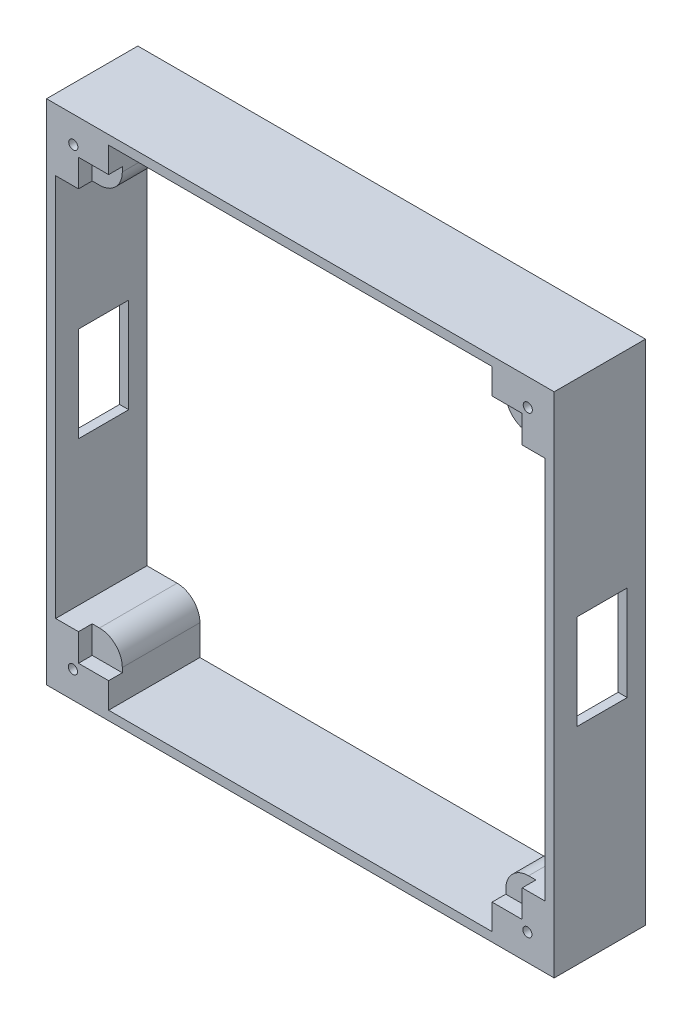
SolidWorks part; units mm, degrees
ref_plane "Přední rovina" through (0, 0, 0) normal (0, 0, 1) x (1, 0, 0)
ref_plane "Horní rovina" through (0, 0, 0) normal (0, 1, 0) x (1, 0, 0)
ref_plane "Pravá rovina" through (0, 0, 0) normal (1, 0, 0) x (0, 0, -1)
sketch "Skica1" plane through (0, 0, 0) normal (0, 0, 1) x (1, 0, 0)
  line L1 (-27.8, 27.8) -> (27.8, 27.8)
  line L2 (-27.8, 27.8) -> (-27.8, -27.8)
  line L3 (-27.8, -27.8) -> (27.8, -27.8)
  line L4 (27.8, 27.8) -> (27.8, -27.8)
  line L5 (-27.8, 27.8) -> (27.8, -27.8) construction
  line L6 (-27.8, -27.8) -> (27.8, 27.8) construction
  line L7 (-26.8, 26.8) -> (26.8, 26.8)
  line L8 (-26.8, 26.8) -> (-26.8, -26.8)
  line L9 (-26.8, -26.8) -> (26.8, -26.8)
  line L10 (26.8, 26.8) -> (26.8, -26.8)
  line L11 (-26.8, 26.8) -> (26.8, -26.8) construction
  line L12 (-26.8, -26.8) -> (26.8, 26.8) construction
  point P0 (0, 0)
  point P5 (0, 0)
  dimension "D1" = 55.6
  dimension "D2" = 53.6
extrude "Přidat vysunutím1" add sketch "Skica1" along normal blind 10
sketch "Skica3" plane through (0, 0, 0) normal (0, 0, -1) x (-1, 0, 0)
  line L0 (26.8, -26.8) -> (21, -26.8)
  line L1 (26.8, 26.8) -> (21, 26.8)
  line L2 (26.8, 26.8) -> (26.8, 21)
  line L3 (26.8, 21) -> (21, 21)
  line L4 (21, 26.8) -> (21, 21)
  line L5 (26.8, -26.8) -> (26.8, -21)
  line L6 (26.8, -21) -> (21, -21)
  line L7 (21, -26.8) -> (21, -21)
  line L8 (-26.8, -26.8) -> (-26.8, -21)
  line L9 (-26.8, -26.8) -> (-21, -26.8)
  line L10 (-21, -26.8) -> (-21, -21)
  line L11 (-26.8, -21) -> (-21, -21)
  line L12 (-26.8, 26.8) -> (-21, 26.8)
  line L13 (-26.8, 26.8) -> (-26.8, 21)
  line L14 (-26.8, 21) -> (-21, 21)
  line L15 (-21, 26.8) -> (-21, 21)
  point P20 (0, 0)
  dimension "D1" = 5.8
  dimension "D2" = 4
extrude "Přidat vysunutím2" add sketch "Skica3" against normal blind 10
fillet "Zaoblit1" radius 2.5 4 edges at (21, 21, 5) (21, -21, 5) (-21, -21, 5) (-21, 21, 5)
sketch "Skica4" plane through (0, 0, 0) normal (0, 0, -1) x (-1, 0, 0)
  line L0 (-27.8, 27.8) -> (27.8, 27.8) construction
  line L1 (27.8, 27.8) -> (27.8, -27.8) construction
  circle A0 centre (23.9, 23.9) radius 2.4
  circle A1 centre (23.9, -23.9) radius 2.4
  circle A2 centre (-23.9, -23.9) radius 2.4
  circle A3 centre (-23.9, 23.9) radius 2.4
  point P15 (0, 0)
  dimension "D1" = 4.8
  dimension "D2" = 3.9
  dimension "D3" = 3.9
  dimension "D4" = 4
extrude "Odebrat vysunutím1" cut sketch "Skica4" against normal blind 8
sketch "Skica5" plane through (0, 0, 8) normal (0, 0, -1) x (-1, 0, 0)
  circle A5 centre (24.869, 24.9105) radius 0.5
  circle A6 centre (-24.9105, 24.869) radius 0.5
  circle A7 centre (-23.9, 23.9) radius 2.4 construction
  circle A8 centre (24.9105, -24.869) radius 0.5
  circle A9 centre (-24.869, -24.9105) radius 0.5
  point P12 (0, 0)
  point P13 (0, 0)
  dimension "D1" = 1
  dimension "D2" = 1.4
  dimension "D3" = 4
extrude "Odebrat vysunutím2" cut sketch "Skica5" against normal blind 2
sketch "Skica6" plane through (0, 0, 10) normal (0, 0, 1) x (1, 0, 0)
  line L1 (-24.3, 24) -> (24.3, 24)
  line L2 (-24.3, 24) -> (-24.3, -24)
  line L3 (-24.3, -24) -> (24.3, -24)
  line L4 (24.3, 24) -> (24.3, -24)
  line L5 (-24.3, 24) -> (24.3, -24) construction
  line L6 (-24.3, -24) -> (24.3, 24) construction
  point P0 (0, 0)
  dimension "D1" = 48
  dimension "D2" = 48.6
extrude "Odebrat vysunutím3" cut sketch "Skica6" against normal blind 1.5
sketch "Skica7" plane through (27.8, 0, 0) normal (1, 0, 0) x (0, 0, -1)
  line L0 (0, -27.8) -> (0, 27.8) construction
  line L1 (-2, 5.2) -> (-7.5, 5.2)
  line L2 (-2, 5.2) -> (-2, -5.2)
  line L3 (-2, -5.2) -> (-7.5, -5.2)
  line L4 (-7.5, 5.2) -> (-7.5, -5.2)
  line L5 (-2, 5.2) -> (-7.5, -5.2) construction
  line L6 (-2, -5.2) -> (-7.5, 5.2) construction
  point P0 (-4.75, 0)
  dimension "D1" = 10.4
  dimension "D2" = 5.5
  dimension "D3" = 2
extrude "Odebrat vysunutím4" cut sketch "Skica7" against normal blind 55.6
